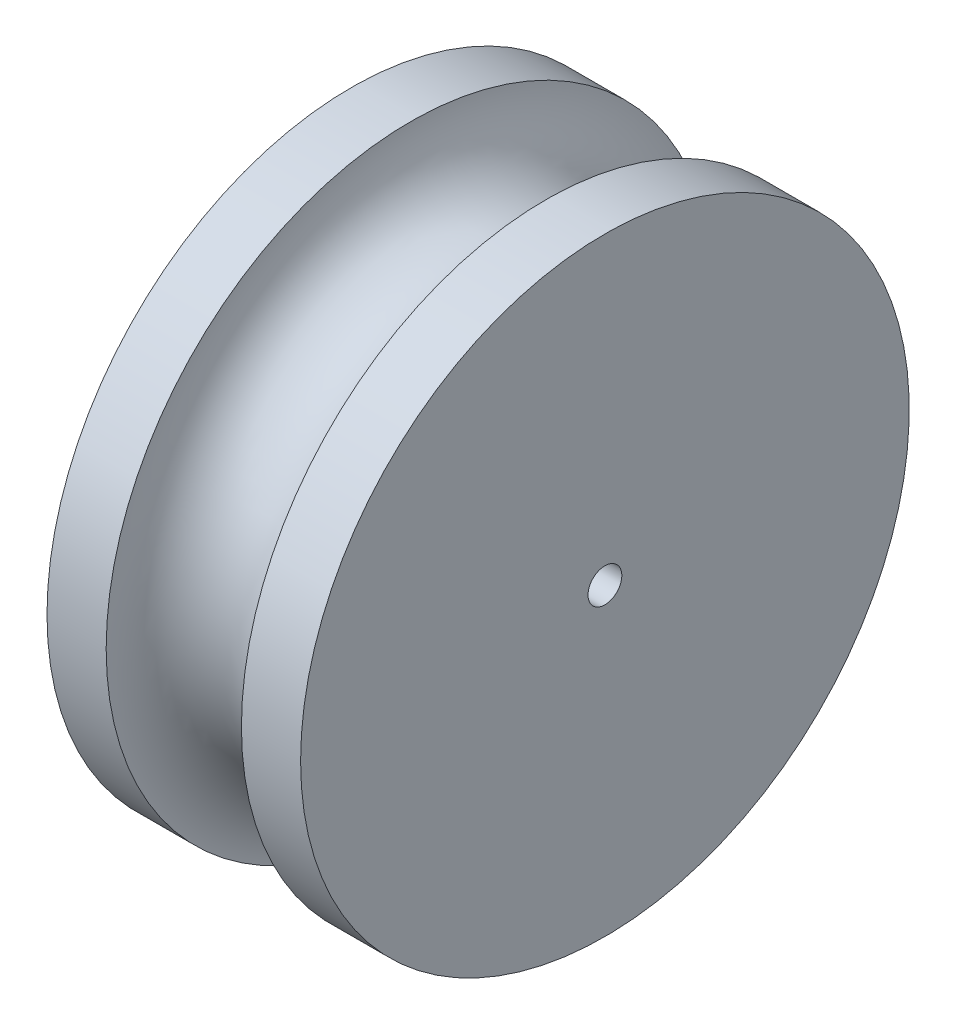
SolidWorks part; units mm, degrees
ref_plane "Front Plane" through (0, 0, 0) normal (0, 0, 1) x (1, 0, 0)
ref_plane "Top Plane" through (0, 0, 0) normal (0, 1, 0) x (1, 0, 0)
ref_plane "Right Plane" through (0, 0, 0) normal (1, 0, 0) x (0, 0, -1)
sketch "Sketch3" plane through (0, 0, 0) normal (0, 1, 0) x (1, 0, 0)
  line L0 (-3583.5896, 0) -> (175595.8881, 0) construction
  line L1 (0, -3583.5896) -> (0, 175595.8881) construction
  line L2 (-95.25, 12.7) -> (-95.25, 228.6)
  line L3 (-95.25, 228.6) -> (-50.8, 228.6)
  line L4 (95.25, 228.6) -> (50.8, 228.6)
  line L5 (95.25, 12.7) -> (95.25, 228.6)
  line L8 (95.25, 12.7) -> (-95.25, 12.7)
  arc A0 (-50.8, 228.6) -> (50.8, 228.6) centre (0, 228.6) ccw
  point P4 (95.25, 25.4)
  point P13 (0, 0)
  point P14 (0, 0)
  dimension "D3" = 50.8
  dimension "D1" = 95.25
  dimension "D2" = 12.7
  dimension "D4" = 228.6
revolve "Revolve1" add sketch "Sketch3" angle 360 about L0
